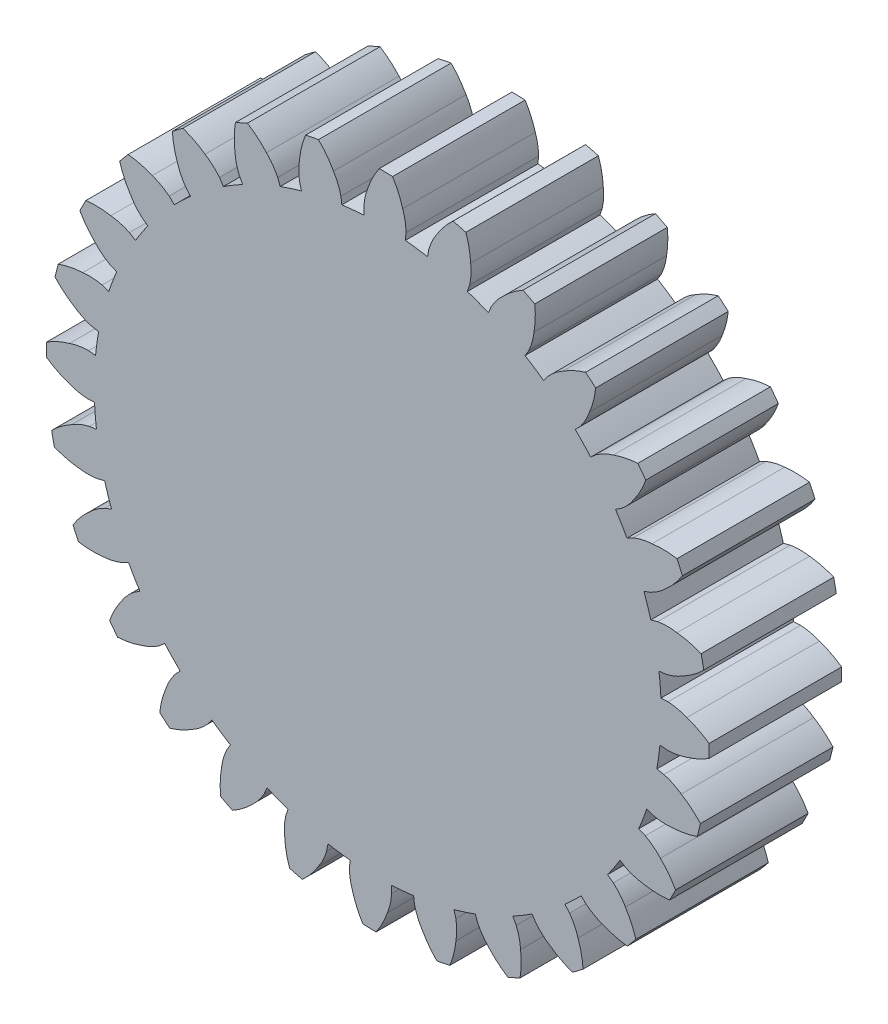
SolidWorks part; units mm, degrees
ref_plane "Plano frontal" through (0, 0, 0) normal (0, 0, 1) x (1, 0, 0)
ref_plane "Plano superior" through (0, 0, 0) normal (0, 1, 0) x (1, 0, 0)
ref_plane "Plano direito" through (0, 0, 0) normal (1, 0, 0) x (0, 0, -1)
sketch "Esboço2" plane through (0, 0, 0) normal (0, 0, 1) x (1, 0, 0)
  line L5 (513.5002, 1211.1934) -> (500.912, 1181.5016)
  line L6 (683.423, 1124.1018) -> (666.6692, 1096.545)
  arc A0 (500.912, 1181.5016) -> (666.6692, 1096.545) centre (0, 0) ccw
  arc A1 (513.5002, 1211.1934) -> (505.1747, 1214.6894) centre (0, 0) ccw
  arc A3 (710.6673, 1320.9663) -> (657.4092, 1348.263) centre (0, 0) ccw
  arc A4 (707.4169, 1208.1231) -> (683.423, 1124.1018) centre (449.9446, 1236.2126) cw
  arc A5 (707.4169, 1208.1231) -> (710.6673, 1320.9663) centre (321.288, 1275.7138) ccw
  arc A6 (567.6994, 1279.7333) -> (513.5002, 1211.1934) centre (740.8451, 1087.1156) ccw
  arc A7 (567.6994, 1279.7333) -> (657.4092, 1348.263) centre (848.0373, 1005.7358) cw
  dimension "D1" = 2566.6
  dimension "D2" = 2631.1
  dimension "D4" = 3000
  dimension "D6" = 259
  dimension "D7" = 392
  dimension "D8" = 157
extrude "Ressalto-extrusão1" add sketch "Esboço2" along normal mid plane 600 contours L5 A0 L6 A4 A5 A3 A7 A6
pattern_circular "PadrãoCircular1" count 28 over 360 about axis through (0, 0, 0) along (0, 0, 1) of "Ressalto-extrusão1"
